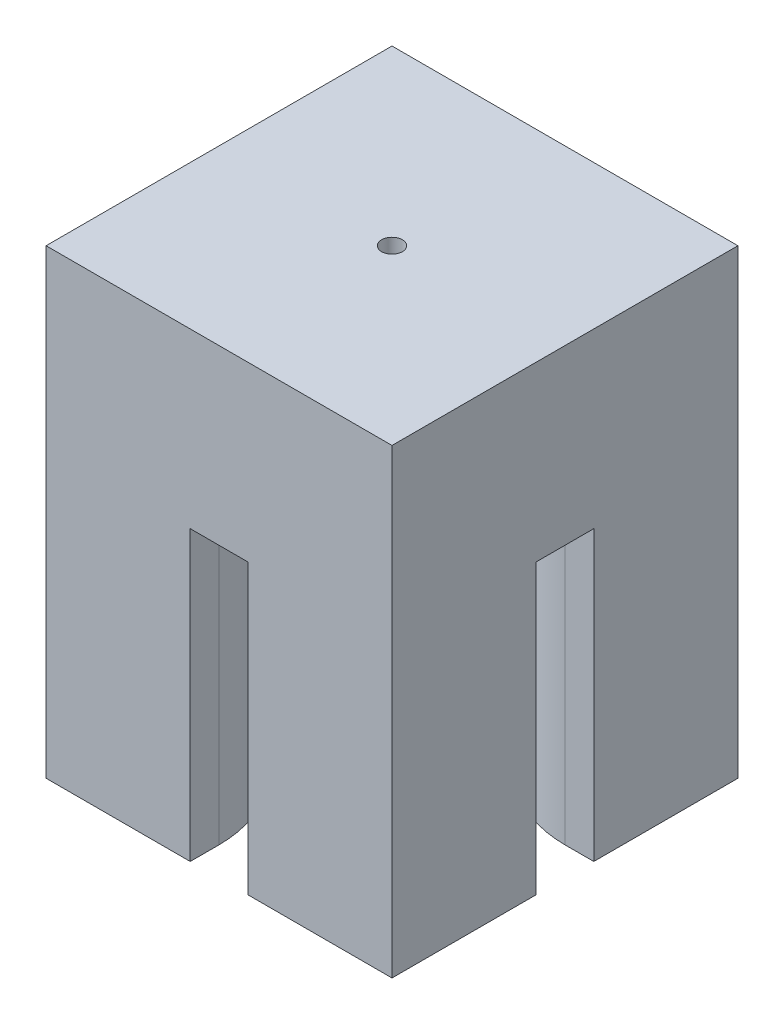
SolidWorks part; units mm, degrees
ref_plane "Front Plane" through (0, 0, 0) normal (0, 0, 1) x (1, 0, 0)
ref_plane "Top Plane" through (0, 0, 0) normal (0, 1, 0) x (1, 0, 0)
ref_plane "Right Plane" through (0, 0, 0) normal (1, 0, 0) x (0, 0, -1)
sketch "Sketch1" plane through (0, 0, 0) normal (0, 1, 0) x (1, 0, 0)
  line L1 (-15, 15) -> (15, 15)
  line L2 (-15, 15) -> (-15, -15)
  line L3 (-15, -15) -> (15, -15)
  line L4 (15, 15) -> (15, -15)
  line L5 (-15, 15) -> (15, -15) construction
  line L6 (-15, -15) -> (15, 15) construction
  point P0 (0, 0)
  dimension "D1" = 30
  dimension "D2" = 30
extrude "Boss-Extrude1" add sketch "Sketch1" along normal blind 40
sketch "Sketch2" plane through (0, 40, 0) normal (0, 1, 0) x (1, 0, 0)
  circle A0 centre (0, 0) radius 0.9
  dimension "D1" = 1.8
extrude "Cut-Extrude1" cut sketch "Sketch2" against normal up to next
sketch "Sketch3" plane through (0, 0, -15) normal (0, 0, -1) x (-1, 0, 0)
  line L0 (-15, 0) -> (15, 0) construction
  line L1 (-2.5, 25) -> (2.5, 25)
  line L2 (-2.5, 25) -> (-2.5, 0)
  line L3 (-2.5, 0) -> (2.5, 0)
  line L4 (2.5, 25) -> (2.5, 0)
  point P7 (0, 0)
  dimension "D1" = 5
  dimension "D2" = 25
extrude "Cut-Extrude2" cut sketch "Sketch3" against normal up to next
sketch "Sketch4" plane through (15, 0, 0) normal (1, 0, 0) x (0, 0, -1)
  line L0 (-15, 0) -> (15, 0) construction
  line L1 (-2.5, 0) -> (2.5, 0)
  line L2 (-2.5, 0) -> (-2.5, 25)
  line L3 (-2.5, 25) -> (2.5, 25)
  line L4 (2.5, 0) -> (2.5, 25)
  point P6 (0, 0)
  dimension "D1" = 5
  dimension "D2" = 25
extrude "Cut-Extrude3" cut sketch "Sketch4" against normal up to surface (30 mm away) up to face at (-15, 20, 0)
fillet "Fillet1" radius 10 4 edges at (2.5, 12.5, -2.5) (2.5, 12.5, 2.5) (-2.5, 12.5, 2.5) (-2.5, 12.5, -2.5)
